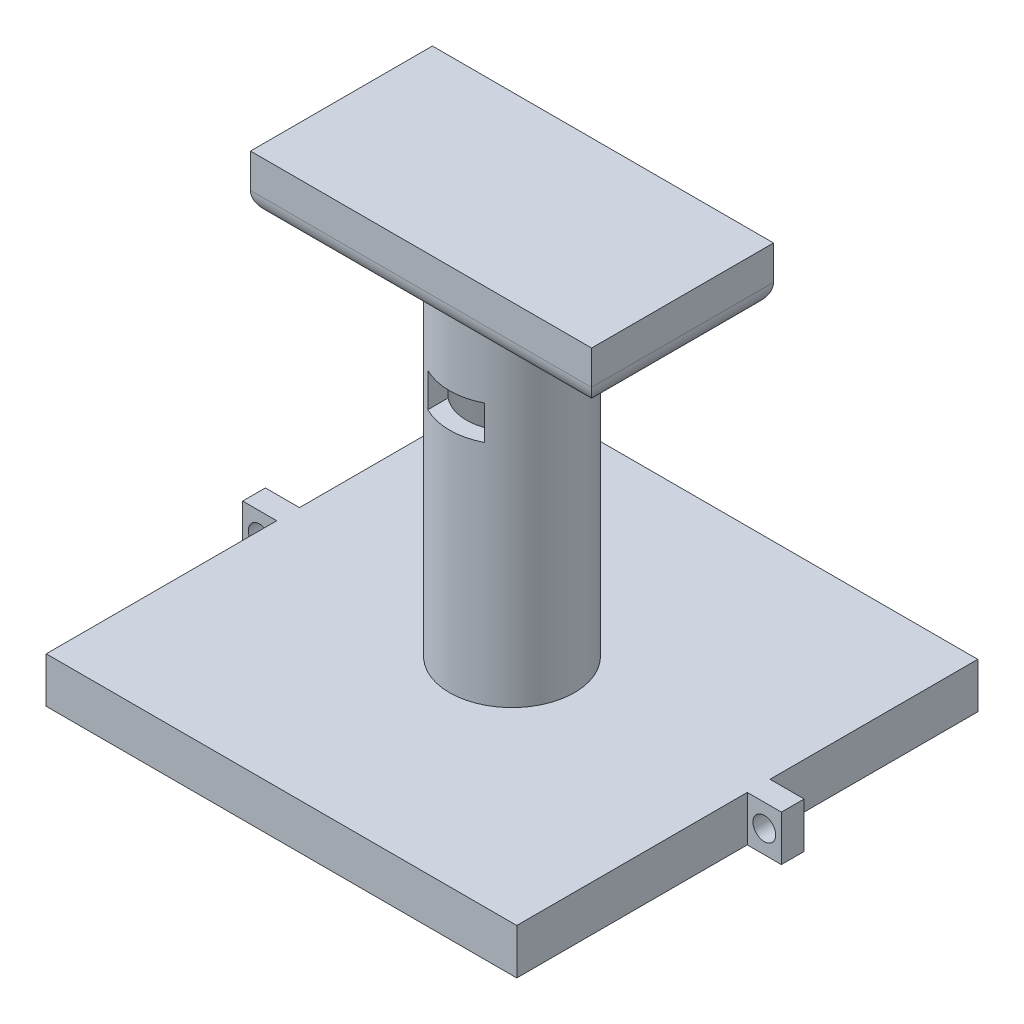
SolidWorks part; units mm, degrees
ref_plane "Front Plane" through (0, 0, 0) normal (0, 0, 1) x (1, 0, 0)
ref_plane "Top Plane" through (0, 0, 0) normal (0, 1, 0) x (1, 0, 0)
ref_plane "Right Plane" through (0, 0, 0) normal (1, 0, 0) x (0, 0, -1)
sketch "Sketch2" plane through (0, 0, 0) normal (0, 1, 0) x (1, 0, 0)
  line L0 (-26.2754, 25.743) -> (26.2754, 25.743)
  line L1 (-26.2754, 25.743) -> (-26.2754, -25.743)
  line L2 (26.2754, 25.743) -> (26.2754, -25.743)
  line L3 (-26.2754, -25.743) -> (26.2754, -25.743)
  line L12 (26.2754, 0) -> (26.2754, 2.54)
  line L13 (26.2754, 0) -> (30.0854, 0)
  line L14 (26.2754, 2.54) -> (30.0854, 2.54)
  line L15 (30.0854, 0) -> (30.0854, 2.54)
  line L16 (-26.2754, 2.54) -> (-26.2754, 0)
  line L17 (-26.2754, 2.54) -> (-30.0854, 2.54)
  line L18 (-26.2754, 0) -> (-30.0854, 0)
  line L19 (-30.0854, 2.54) -> (-30.0854, 0)
  dimension "D1" = 52.5507
  dimension "D2" = 51.486
  dimension "D3" = 25.743
  dimension "D4" = 25.743
  dimension "D5" = 2.54
  dimension "D6" = 3.81
  dimension "D7" = 26.2754
  dimension "D8" = 3.81
  dimension "D9" = 2.54
  dimension "D10" = 25.743
extrude "Boss-Extrude1" add sketch "Sketch2" along normal blind 5.08
sketch "Sketch3" plane through (0, 0, 0) normal (0, -1, 0) x (1, 0, 0)
  line L0 (23.7354, -23.203) -> (23.7354, 23.203)
  line L1 (23.7354, -23.203) -> (-23.7354, -23.203)
  line L2 (23.7354, 23.203) -> (-23.7354, 23.203)
  line L3 (-23.7354, -23.203) -> (-23.7354, 23.203)
  line L4 (-26.2754, 25.743) -> (26.2754, 25.743) construction
  line L5 (-26.2754, -25.743) -> (26.2754, -25.743) construction
  line L7 (-26.2754, -25.743) -> (-26.2754, -2.54) construction
  line L8 (26.2754, -25.743) -> (26.2754, -2.54) construction
  dimension "D1" = 2.54
  dimension "D2" = 2.54
  dimension "D3" = 2.54
  dimension "D4" = 2.54
extrude "Cut-Extrude1" cut sketch "Sketch3" against normal blind 3.81
ref_plane "Plane1" through (0, 0, 0) normal (0, 0, 1) x (1, 0, 0)
sketch "Sketch4" plane through (0, 0, 0) normal (0, 0, 1) x (1, 0, 0)
  line L0 (28.1804, 0) -> (28.1804, 5.08) construction
  line L1 (26.2754, 0) -> (30.0854, 0) construction
  line L2 (26.2754, 5.08) -> (30.0854, 5.08) construction
  line L3 (0, 5.08) -> (0, 0) construction
  line L4 (-26.2754, 5.08) -> (26.2754, 5.08) construction
  line L5 (-26.2754, 0) -> (26.2754, 0) construction
  circle A0 centre (28.1804, 2.54) radius 1.27
  circle A1 centre (-28.1804, 2.54) radius 1.27
  dimension "D1" = 2.54
extrude "Cut-Extrude2" cut sketch "Sketch4" against normal blind 3.302
sketch "Sketch5" plane through (0, 5.08, 0) normal (0, 1, 0) x (1, 0, 0)
  circle A0 centre (0, 0) radius 5.08
  dimension "D1" = 10.16
extrude "Cut-Extrude3" cut sketch "Sketch5" against normal blind 1.9304
sketch "Sketch6" plane through (0, 5.08, 0) normal (0, 1, 0) x (1, 0, 0)
  circle A0 centre (0, 0) radius 6.985
  dimension "D1" = 13.97
extrude "Boss-Extrude2" add sketch "Sketch6" along normal blind 38.1
sketch "Sketch8" plane through (0, 43.18, 0) normal (0, 1, 0) x (1, 0, 0)
  circle A0 centre (0, 0) radius 5.08
  dimension "D1" = 10.16
extrude "Cut-Extrude4" cut sketch "Sketch8" against normal blind 38.1
sketch "Sketch7" plane through (0, 43.18, 0) normal (0, 1, 0) x (1, 0, 0)
  line L0 (-19.05, -10.16) -> (19.05, -10.16)
  line L1 (-19.05, -10.16) -> (-19.05, 10.16)
  line L2 (19.05, -10.16) -> (19.05, 10.16)
  line L3 (-19.05, 10.16) -> (19.05, 10.16)
  dimension "D1" = 19.05
  dimension "D2" = 38.1
  dimension "D3" = 10.16
  dimension "D4" = 20.32
extrude "Boss-Extrude3" add sketch "Sketch7" along normal blind 6.35
fillet "Fillet3" radius 2.54 4 edges at (19.05, 43.18, 0) (0, 43.18, -10.16) (-19.05, 43.18, 0) (0, 43.18, 10.16)
ref_plane "Plane2" through (0, 0, 0.343) normal (0, 0, 1) x (1, 0, 0)
sketch "Sketch9" plane through (0, 0, 0.343) normal (0, 0, 1) x (1, 0, 0)
  line L0 (3.175, 30.48) -> (3.175, 34.29)
  line L1 (3.175, 30.48) -> (-3.175, 30.48)
  line L2 (3.175, 34.29) -> (-3.175, 34.29)
  line L3 (-3.175, 30.48) -> (-3.175, 34.29)
  line L4 (16.51, 43.18) -> (-16.51, 43.18) construction
  line L5 (6.985, 5.08) -> (6.985, 43.18) construction
  dimension "D1" = 6.35
  dimension "D2" = 3.81
  dimension "D3" = 8.89
  dimension "D4" = 3.81
extrude "Cut-Extrude5" cut sketch "Sketch9" along normal blind 11.938
